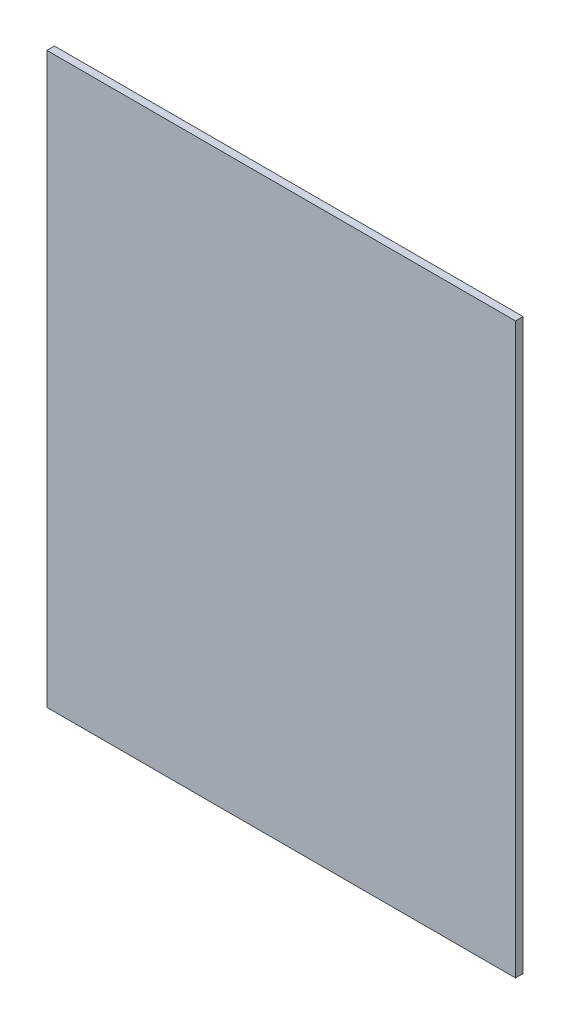
SolidWorks part; units mm, degrees
ref_plane "Front Plane" through (0, 0, 0) normal (0, 0, 1) x (1, 0, 0)
ref_plane "Top Plane" through (0, 0, 0) normal (0, 1, 0) x (1, 0, 0)
ref_plane "Right Plane" through (0, 0, 0) normal (1, 0, 0) x (0, 0, -1)
sketch "Sketch1" plane through (0, 0, 0) normal (0, 0, 1) x (1, 0, 0)
  line L1 (-98.425, -119.5) -> (98.425, -119.5)
  line L2 (-98.425, -119.5) -> (-98.425, 119.5)
  line L3 (-98.425, 119.5) -> (98.425, 119.5)
  line L4 (98.425, -119.5) -> (98.425, 119.5)
  line L5 (-98.425, -119.5) -> (98.425, 119.5) construction
  line L6 (-98.425, 119.5) -> (98.425, -119.5) construction
  point P0 (0, 0)
  dimension "D1" = 196.85
  dimension "D2" = 239
extrude "Boss-Extrude1" add sketch "Sketch1" along normal blind 3.175
